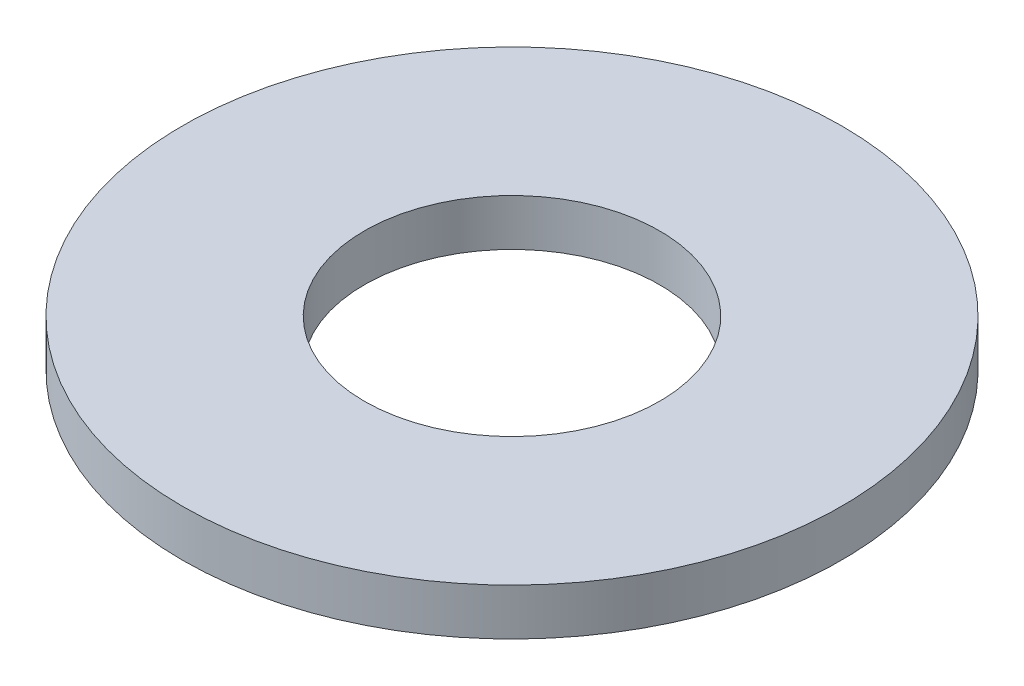
SolidWorks part; units mm, degrees
ref_plane "Front Plane" through (0, 0, 0) normal (0, 0, 1) x (1, 0, 0)
ref_plane "Top Plane" through (0, 0, 0) normal (0, 1, 0) x (1, 0, 0)
ref_plane "Right Plane" through (0, 0, 0) normal (1, 0, 0) x (0, 0, -1)
sketch "Sketch1" plane through (0, 0, 0) normal (0, 1, 0) x (1, 0, 0)
  circle A0 centre (0, 0) radius 11.1125
  circle A1 centre (0, 0) radius 4.9784
  dimension "D1" = 22.225
  dimension "D2" = 9.9568
extrude "Boss-Extrude1" add sketch "Sketch1" along normal blind 1.5748
